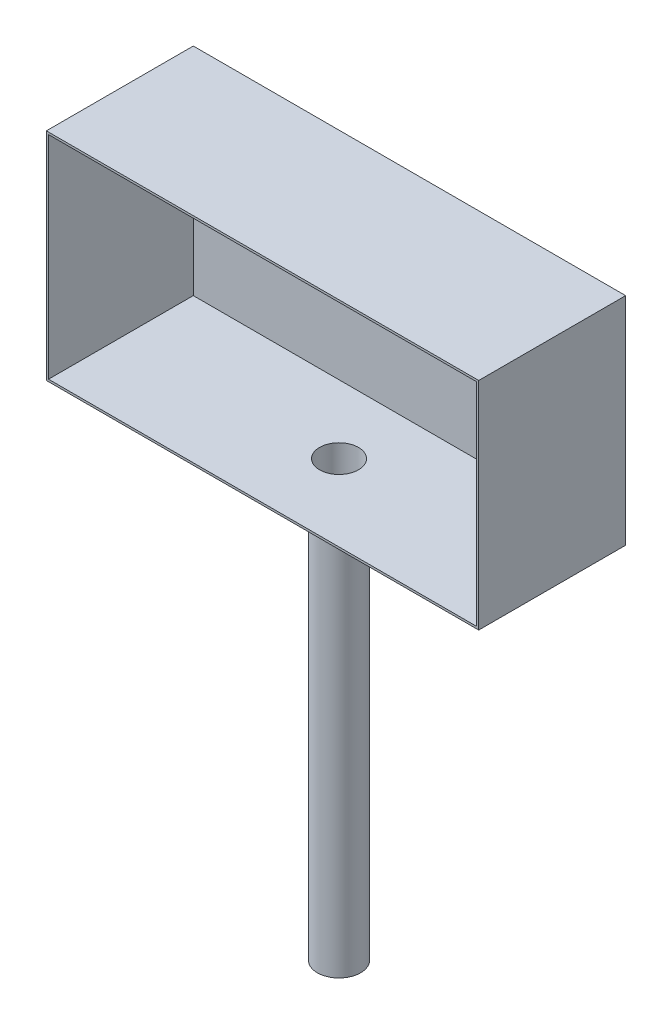
SolidWorks part; units mm, degrees
ref_plane "Front Plane" through (0, 0, 0) normal (0, 0, 1) x (1, 0, 0)
ref_plane "Top Plane" through (0, 0, 0) normal (0, 1, 0) x (1, 0, 0)
ref_plane "Right Plane" through (0, 0, 0) normal (1, 0, 0) x (0, 0, -1)
sketch "Sketch2" plane through (0, 0, 0) normal (0, 1, 0) x (1, 0, 0)
  circle A0 centre (0, 0) radius 100
extrude "Boss-Extrude1" add sketch "Sketch2" along normal blind 2000
sketch "Sketch3" plane through (0, 0, 0) normal (1, 0, 0) x (0, 0, -1)
  line L0 (0, 2000) -> (-353.7193, 2000)
  line L1 (100, 2000) -> (-100, 2000) construction
  line L2 (-353.7193, 2000) -> (-353.7193, 3000)
  line L3 (-353.7193, 3000) -> (325.945, 3000)
  line L4 (325.945, 3000) -> (325.945, 2000)
  line L5 (325.945, 2000) -> (0, 2000)
  dimension "D1" = 1000
extrude "Boss-Extrude2" add sketch "Sketch3" along normal mid plane 2000
shell "Shell1" thickness 10
